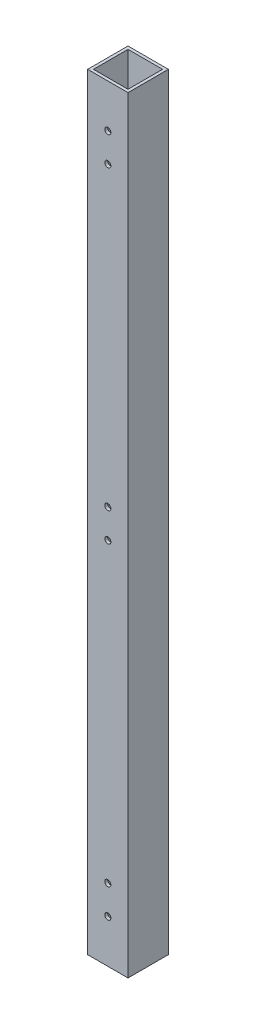
SolidWorks part; units mm, degrees
material "6061 Alloy"
ref_plane "Front Plane" through (0, 0, 0) normal (0, 0, 1) x (1, 0, 0)
ref_plane "Top Plane" through (0, 0, 0) normal (0, 1, 0) x (1, 0, 0)
ref_plane "Right Plane" through (0, 0, 0) normal (1, 0, 0) x (0, 0, -1)
sketch "Sketch1" plane through (0, 0, 0) normal (0, 1, 0) x (1, 0, 0)
  line L1 (0, 0) -> (44.45, 0)
  line L2 (0, 0) -> (0, 44.45)
  line L3 (0, 44.45) -> (44.45, 44.45)
  line L4 (44.45, 0) -> (44.45, 44.45)
  line L5 (3.175, 41.275) -> (41.275, 41.275)
  line L6 (3.175, 41.275) -> (3.175, 3.175)
  line L7 (3.175, 3.175) -> (41.275, 3.175)
  line L8 (41.275, 41.275) -> (41.275, 3.175)
  dimension "D1" = 38.1
  dimension "D2" = 3.175
  dimension "D3" = 3.175
  dimension "D4" = 38.1
  dimension "D5" = 44.45
  dimension "D6" = 44.45
extrude "Boss-Extrude1" add sketch "Sketch1" along normal blind 844.55
hole_wizard "17/64 (0.26563) Diameter Hole1" positions "Sketch2" profile "Sketch3" hole size "17/64" standard "ANSI Inch" end condition through all
sketch "Sketch2" plane through (0, 0, 0) normal (0, 0, 1) x (1, 0, 0)
  line L0 (0, 844.55) -> (44.45, 844.55) construction
  line L1 (0, 422.275) -> (44.45, 422.275) construction
  line L2 (0, 844.55) -> (0, 0) construction
  line L3 (44.45, 844.55) -> (44.45, 0) construction
  point P0 (22.225, 796.925)
  point P2 (22.225, 765.175)
  point P4 (22.225, 438.15)
  point P29 (22.225, 406.4)
  point P30 (22.225, 79.375)
  point P31 (22.225, 47.625)
  dimension "D1" = 31.75
  dimension "D2" = 47.625
  dimension "D3" = 22.225
  dimension "D4" = 15.875
sketch "Sketch3" plane through (22.225, 796.925, 0) normal (1, 0, 0) x (0, -1, 0)
  line L0 (0, 0) -> (0, 44.45)
  line L1 (0, 44.45) -> (3.3735, 44.45)
  line L2 (3.3735, 44.45) -> (3.3735, 0)
  line L5 (3.3735, 0) -> (0, 0)
  line L11 (0, -6.35) -> (0, 107.95) construction
  dimension "Thru Hole Dia." = 6.747
  dimension "Thru Hole Depth" = 44.45
